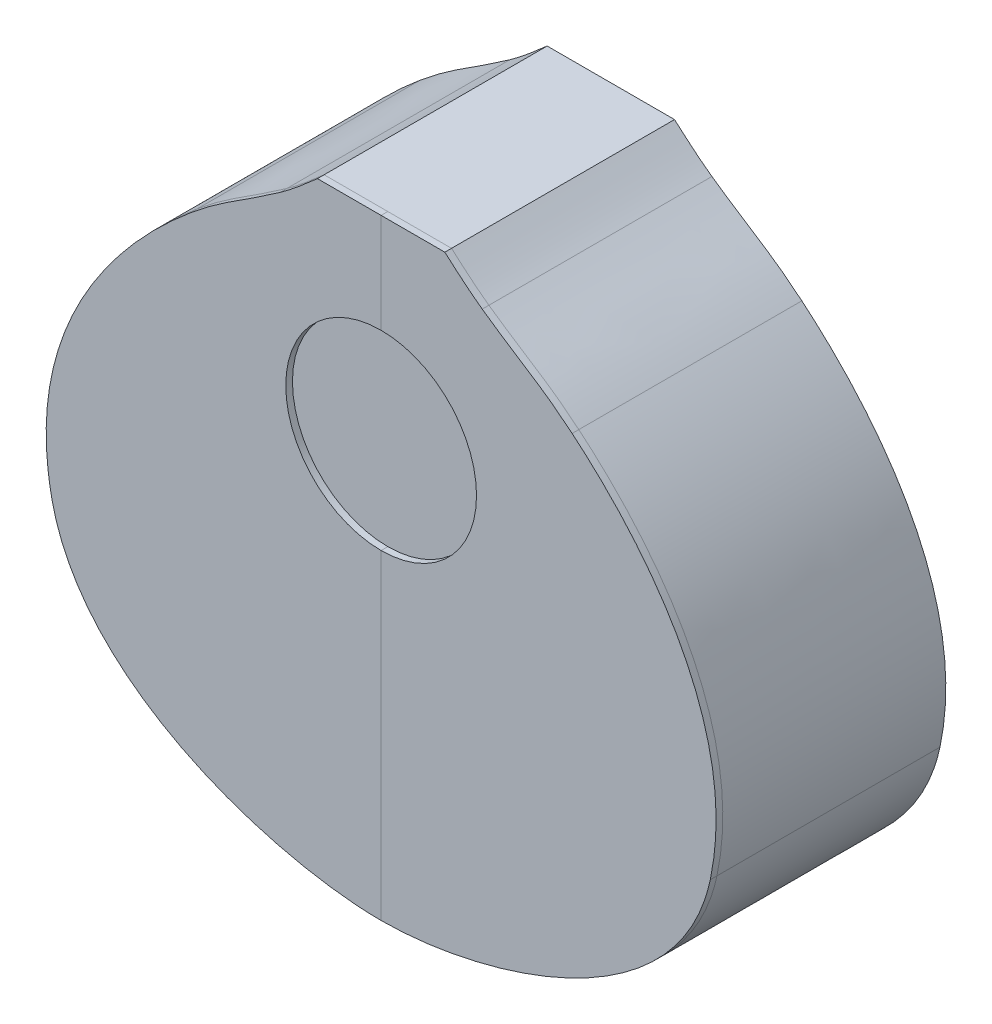
SolidWorks part; units mm, degrees
ref_plane "Alzado" through (0, 0, 0) normal (0, 0, 1) x (1, 0, 0)
ref_plane "Planta" through (0, 0, 0) normal (0, 1, 0) x (1, 0, 0)
ref_plane "Vista lateral" through (0, 0, 0) normal (1, 0, 0) x (0, 0, -1)
sketch "Croquis1" plane through (0, 0, 0) normal (0, 0, 1) x (1, 0, 0)
  line L0 (-28.5608, 136.9164) -> (0, 136.9164)
  line L3 (0, 136.9164) -> (0, -136.9164)
  spline S0 degree 3 poles (-147.5785, -47.2765) (-163.1102, 25.4873) (-105.3607, 78.5809) (-85.6394, 95.0588) knots 0 0 0 0 1 1 1 1
  spline S1 degree 3 poles (-85.6394, 95.0588) (-70.7787, 107.4754) (-62.7858, 110.8395) (-45.3232, 123.1886) knots 0 0 0 0 1 1 1 1
  spline S2 degree 3 poles (-45.3232, 123.1886) (-39.5023, 127.305) (-33.9335, 132.1947) (-28.5608, 136.9164) knots 0 0 0 0 1 1 1 1
  spline S7 degree 3 poles (0, -136.9164) (-46.4413, -136.9164) (-133.8334, -111.6704) (-147.5785, -47.2765) knots 0 0 0 0 1 1 1 1
  dimension "D1" = 273.8328
sketch "Croquis3" plane through (0, 0, 0) normal (0, 0, 1) x (1, 0, 0)
  line L0 (0, 136.9164) -> (0, -136.9164)
  line L1 (0, 136.9164) -> (28.5608, 136.9164)
  spline S0 degree 3 poles (0, -136.9164) (46.4413, -136.9164) (133.8334, -111.6704) (147.5785, -47.2765) knots 0 0 0 0 1 1 1 1
  spline S1 degree 3 poles (147.5785, -47.2765) (163.1102, 25.4873) (105.3607, 78.5809) (85.6394, 95.0588) knots 0 0 0 0 1 1 1 1
  spline S2 degree 3 poles (85.6394, 95.0588) (70.7787, 107.4754) (62.7858, 110.8395) (45.3232, 123.1886) knots 0 0 0 0 1 1 1 1
  spline S3 degree 3 poles (45.3232, 123.1886) (39.5023, 127.305) (33.9335, 132.1947) (28.5608, 136.9164) knots 0 0 0 0 1 1 1 1
extrude "Saliente-Extruir1" add sketch "Croquis1" along normal blind 100
extrude "Saliente-Extruir2" add sketch "Croquis3" along normal blind 100
sketch "Croquis8" plane through (0, 0, 100) normal (0, 0, 1) x (1, 0, 0)
  line L0 (28.5608, 136.9164) -> (-28.5608, 136.9164) construction
  line B0 (0, 6.7699) -> (0, -136.9164)
  line B1 (0, 136.9164) -> (0, 92.3065)
  line B2 (28.5608, 136.9164) -> (0, 136.9164)
  arc B3 (0, 92.3065) -> (0, 6.7699) centre (0, 49.5382) cw
  spline B4 degree 3 poles (0, -136.9164) (46.4413, -136.9164) (133.8334, -111.6704) (147.5785, -47.2765) knots 0 0 0 0 1 1 1 1
  spline B5 degree 3 poles (45.3232, 123.1886) (39.5023, 127.305) (33.9335, 132.1947) (28.5608, 136.9164) knots 0 0 0 0 1 1 1 1
  spline B6 degree 3 poles (85.6394, 95.0588) (70.7787, 107.4754) (62.7858, 110.8395) (45.3232, 123.1886) knots 0 0 0 0 1 1 1 1
  spline B7 degree 3 poles (147.5785, -47.2765) (163.1102, 25.4873) (105.3607, 78.5809) (85.6394, 95.0588) knots 0 0 0 0 1 1 1 1
sketch_block_instance "Bloque4-1"
sketch_block "Bloque4"
sketch "Croquis10" plane through (0, 0, 100) normal (0, 0, 1) x (1, 0, 0)
  line B0 (-28.5608, 136.9164) -> (0, 136.9164)
  line B1 (0, 136.9164) -> (0, 92.3065)
  line B2 (0, 6.7699) -> (0, -136.9164)
  line B3 (0, 6.7699) -> (0, 92.3065) construction
  arc B4 (0, 92.3065) -> (0, 6.7699) centre (0, 49.5382) ccw
  spline B5 degree 3 poles (-147.5785, -47.2765) (-163.1102, 25.4873) (-105.3607, 78.5809) (-85.6394, 95.0588) knots 0 0 0 0 1 1 1 1
  spline B6 degree 3 poles (-85.6394, 95.0588) (-70.7787, 107.4754) (-62.7858, 110.8395) (-45.3232, 123.1886) knots 0 0 0 0 1 1 1 1
  spline B7 degree 3 poles (-45.3232, 123.1886) (-39.5023, 127.305) (-33.9335, 132.1947) (-28.5608, 136.9164) knots 0 0 0 0 1 1 1 1
  spline B8 degree 3 poles (0, -136.9164) (-46.4413, -136.9164) (-133.8334, -111.6704) (-147.5785, -47.2765) knots 0 0 0 0 1 1 1 1
sketch_block_instance "Bloque5-1"
sketch_block "Bloque5"
extrude "Saliente-Extruir6" add sketch "Croquis10" along normal blind 3 separate body
extrude "Saliente-Extruir7" add sketch "Croquis8" along normal blind 3 separate body
